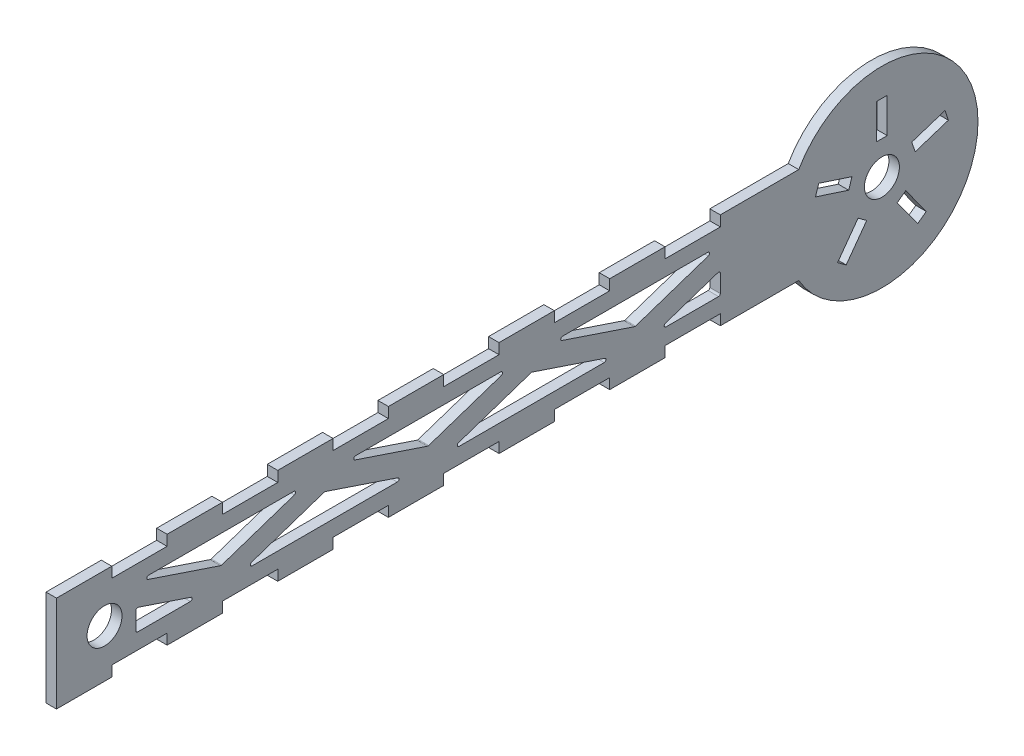
SolidWorks part; units mm, degrees
other "Markup1"
sketch "Sketch2" plane through (3, 13.75, 150) normal (0.7954, 0.3724, 0.4781) x (0.4726, 0.1125, -0.874)
ref_plane "Front Plane" through (0, 0, 0) normal (0, 0, 1) x (1, 0, 0)
ref_plane "Top Plane" through (0, 0, 0) normal (0, 1, 0) x (1, 0, 0)
ref_plane "Right Plane" through (0, 0, 0) normal (1, 0, 0) x (0, 0, -1)
sketch "Sketch1" plane through (0, 0, 0) normal (1, 0, 0) x (0, 0, -1)
  line L0 (65, -13.75) -> (65, 13.75) construction
  line L1 (-125, -13.75) -> (125, -13.75)
  line L2 (-125, -13.75) -> (-125, 13.75)
  line L3 (-125, 13.75) -> (125, 13.75)
  line L4 (125, -13.75) -> (125, 13.75)
  line L5 (-125, -13.75) -> (125, 13.75) construction
  line L6 (-125, 13.75) -> (125, -13.75) construction
  line L11 (119.8138, 4.386) -> (129.3244, 7.4762)
  line L13 (-125, 10.75) -> (-109.1667, 10.75) construction
  line L14 (-109.1667, 10.75) -> (-93.3333, 10.75)
  line L15 (-109.1667, 10.75) -> (-109.1667, 13.75)
  line L16 (-109.1667, 13.75) -> (-93.3333, 13.75)
  line L17 (-93.3333, 10.75) -> (-93.3333, 13.75)
  line L18 (-109.1667, 10.75) -> (-93.3333, 13.75) construction
  line L19 (-109.1667, 13.75) -> (-93.3333, 10.75) construction
  line L20 (-77.5, 10.75) -> (-61.6667, 10.75)
  line L21 (-77.5, 10.75) -> (-77.5, 13.75)
  line L22 (-77.5, 13.75) -> (-61.6667, 13.75)
  line L23 (-61.6667, 10.75) -> (-61.6667, 13.75)
  line L24 (-77.5, 10.75) -> (-61.6667, 13.75) construction
  line L25 (-77.5, 13.75) -> (-61.6667, 10.75) construction
  line L26 (-45.8333, 10.75) -> (-30, 10.75)
  line L27 (-45.8333, 10.75) -> (-45.8333, 13.75)
  line L28 (-45.8333, 13.75) -> (-30, 13.75)
  line L29 (-30, 10.75) -> (-30, 13.75)
  line L30 (-45.8333, 10.75) -> (-30, 13.75) construction
  line L31 (-45.8333, 13.75) -> (-30, 10.75) construction
  line L32 (-14.1667, 10.75) -> (1.6667, 10.75)
  line L33 (-14.1667, 10.75) -> (-14.1667, 13.75)
  line L34 (-14.1667, 13.75) -> (1.6667, 13.75)
  line L35 (1.6667, 10.75) -> (1.6667, 13.75)
  line L36 (-14.1667, 10.75) -> (1.6667, 13.75) construction
  line L37 (-14.1667, 13.75) -> (1.6667, 10.75) construction
  line L38 (17.5, 10.75) -> (33.3333, 10.75)
  line L39 (17.5, 10.75) -> (17.5, 13.75)
  line L40 (17.5, 13.75) -> (33.3333, 13.75)
  line L41 (33.3333, 10.75) -> (33.3333, 13.75)
  line L42 (17.5, 10.75) -> (33.3333, 13.75) construction
  line L43 (17.5, 13.75) -> (33.3333, 10.75) construction
  line L44 (49.1667, 10.75) -> (65, 10.75)
  line L45 (49.1667, 10.75) -> (49.1667, 13.75)
  line L46 (49.1667, 13.75) -> (65, 13.75)
  line L47 (65, 10.75) -> (65, 13.75)
  line L48 (49.1667, 10.75) -> (65, 13.75) construction
  line L49 (49.1667, 13.75) -> (65, 10.75) construction
  line L50 (-93.3333, 10.75) -> (-77.5, 10.75) construction
  line L51 (-61.6667, 10.75) -> (-45.8333, 10.75) construction
  line L52 (-30, 10.75) -> (-14.1667, 10.75) construction
  line L53 (1.6667, 10.75) -> (17.5, 10.75) construction
  line L54 (33.3333, 10.75) -> (49.1667, 10.75) construction
  line L56 (-125, 0) -> (125, 0) construction
  line L57 (49.1667, -13.75) -> (65, -13.75)
  line L58 (65, -10.75) -> (65, -13.75)
  line L59 (49.1667, -10.75) -> (65, -10.75)
  line L60 (49.1667, -10.75) -> (49.1667, -13.75)
  line L61 (17.5, -13.75) -> (33.3333, -13.75)
  line L62 (33.3333, -10.75) -> (33.3333, -13.75)
  line L63 (17.5, -10.75) -> (33.3333, -10.75)
  line L64 (17.5, -10.75) -> (17.5, -13.75)
  line L65 (-14.1667, -13.75) -> (1.6667, -13.75)
  line L66 (1.6667, -10.75) -> (1.6667, -13.75)
  line L67 (-14.1667, -10.75) -> (1.6667, -10.75)
  line L68 (-14.1667, -10.75) -> (-14.1667, -13.75)
  line L69 (-45.8333, -13.75) -> (-30, -13.75)
  line L70 (-30, -10.75) -> (-30, -13.75)
  line L71 (-45.8333, -10.75) -> (-30, -10.75)
  line L72 (-45.8333, -10.75) -> (-45.8333, -13.75)
  line L73 (-77.5, -13.75) -> (-61.6667, -13.75)
  line L74 (-61.6667, -10.75) -> (-61.6667, -13.75)
  line L75 (-77.5, -10.75) -> (-61.6667, -10.75)
  line L76 (-77.5, -10.75) -> (-77.5, -13.75)
  line L77 (-109.1667, -13.75) -> (-93.3333, -13.75)
  line L78 (-93.3333, -10.75) -> (-93.3333, -13.75)
  line L79 (-109.1667, -10.75) -> (-93.3333, -10.75)
  line L80 (-109.1667, -10.75) -> (-109.1667, -13.75)
  line L83 (109.725, 9.5) -> (112.775, 9.5)
  line L84 (109.725, 9.5) -> (109.725, 19.5)
  line L85 (109.725, 19.5) -> (112.775, 19.5)
  line L86 (112.775, 9.5) -> (112.775, 19.5)
  line L87 (109.725, 9.5) -> (112.775, 19.5) construction
  line L88 (109.725, 19.5) -> (112.775, 9.5) construction
  line L89 (119.8138, 4.386) -> (120.7563, 1.4853)
  line L90 (120.7563, 1.4853) -> (130.2669, 4.5755)
  line L91 (129.3244, 7.4762) -> (130.2669, 4.5755)
  line L92 (118.0677, -6.7893) -> (123.9456, -14.8795)
  line L93 (118.0677, -6.7893) -> (115.6002, -8.582)
  line L94 (115.6002, -8.582) -> (121.4781, -16.6722)
  line L95 (123.9456, -14.8795) -> (121.4781, -16.6722)
  line L96 (106.8998, -8.582) -> (101.0219, -16.6722)
  line L97 (106.8998, -8.582) -> (104.4323, -6.7893)
  line L98 (104.4323, -6.7893) -> (98.5544, -14.8795)
  line L99 (101.0219, -16.6722) -> (98.5544, -14.8795)
  line L100 (101.7437, 1.4853) -> (92.2331, 4.5755)
  line L101 (101.7437, 1.4853) -> (102.6862, 4.386)
  line L102 (102.6862, 4.386) -> (93.1756, 7.4762)
  line L103 (92.2331, 4.5755) -> (93.1756, 7.4762)
  line L104 (111.25, 0) -> (112.775, 9.5) construction
  circle A4 centre (111.25, 0) radius 5
  circle A5 centre (-111.25, 0) radius 5
  circle A7 centre (111.25, 0) radius 27.5
  point P0 (0, 0)
  point P6 (111.25, 14.5)
  point P13 (0, 0)
  point P14 (0, 0)
  point P19 (-101.25, 12.25)
  point P26 (-69.5833, 12.25)
  point P31 (-37.9167, 12.25)
  point P36 (-6.25, 12.25)
  point P41 (25.4167, 12.25)
  point P46 (57.0833, 12.25)
  point P54 (111.25, 0)
  point P96 (0, 0)
  dimension "D2" = 111.25
  dimension "D3" = 10
  dimension "D7" = 10
  dimension "D9" = 55
  dimension "D4" = 65
  dimension "D5" = 27.5
  dimension "D6" = 250
  dimension "D8" = 13.75
  dimension "D10" = 3
  dimension "D11" = 3.05
  dimension "D12" = 10
  dimension "D13" = 14.5
  dimension "D14" = 5
extrude "Boss-Extrude1" add sketch "Sketch1" along normal blind 3 contours L1 A7 L3 L84 L85 L86 L4 L11 L91 L90 L92 L95 L94 L96 L99 L98 | L3 A7 L1 L98 L97 L96 L94 L93 L92 L4 L90 L89 L11 L86 L83 L84 L100 L103 L102 L101 A4 | A7 L3 L47 L44 L45 L41 L38 L39 L35 L32 L33 L29 L26 L27 L23 L20 L21 L17 L14 L15 L2 L1 L80 L79 L78 L76 L75 L74 L72 L71 L70 L68 L67 L66 L64 L63 L62 L60 L59 L58
sketch "Sketch3" plane through (3, 0, 0) normal (1, 0, 0) x (0, 0, -1)
  line L0 (-101.7013, 6.25) -> (-102.25, 6.25) construction
  line L1 (-102.25, -6.25) -> (65, -6.25)
  line L2 (-102.25, -6.25) -> (-102.25, 6.25)
  line L3 (-102.25, 6.25) -> (65, 6.25)
  line L4 (65, -6.25) -> (65, 6.25)
  line L5 (-102.25, -6.25) -> (65, 6.25) construction
  line L6 (-102.25, 6.25) -> (65, -6.25) construction
  line L7 (-102.25, 6.25) -> (-102.25, 10.75) construction
  line L8 (65, 6.25) -> (64.4513, 6.25) construction
  line L9 (-102.25, -6.25) -> (-102.25, -10.75) construction
  line L10 (-102.25, 0) -> (-102.25, 6.25) construction
  line L11 (-102.25, 0) -> (-116.25, 0) construction
  line L12 (65, 10.75) -> (65, 13.75) construction
  line L13 (-109.1667, -10.75) -> (-93.3333, -10.75) construction
  line L14 (-102.25, 0) -> (-83.6184, -6.25)
  line L15 (-101.7013, 6.25) -> (-77.8529, -1.75)
  line L16 (-77.8529, -1.75) -> (-54.0045, 6.25)
  line L17 (-72.0874, -6.25) -> (-48.2389, 1.75)
  line L18 (-48.2389, 1.75) -> (-24.3905, -6.25)
  line L19 (-12.8595, -6.25) -> (10.9889, 1.75)
  line L20 (10.9889, 1.75) -> (34.8374, -6.25)
  line L21 (46.3684, -6.25) -> (65, 0)
  line L22 (-83.6184, -6.25) -> (-72.0874, -6.25) construction
  line L23 (-54.0045, 6.25) -> (-42.4734, 6.25) construction
  line L24 (-42.4734, 6.25) -> (-18.625, -1.75)
  line L25 (-18.625, -1.75) -> (5.2234, 6.25)
  line L26 (16.7545, 6.25) -> (40.6029, -1.75)
  line L27 (40.6029, -1.75) -> (64.4513, 6.25)
  line L28 (-24.3905, -6.25) -> (-12.8595, -6.25) construction
  line L29 (5.2234, 6.25) -> (16.7545, 6.25) construction
  line L30 (34.8374, -6.25) -> (46.3684, -6.25) construction
  line L31 (65, 0) -> (65, 6.25) construction
  circle A0 centre (-111.25, 0) radius 5 construction
  point P0 (-18.625, 0)
  point P18 (85.2212, 0)
  point P23 (0, 0)
  point P32 (0, 0)
  dimension "D1" = 4.5
  dimension "D2" = 14
  dimension "D3" = 6.1
  dimension "D4" = 8
extrude "Cut-Extrude1" cut sketch "Sketch3" against normal blind 3 contours L14 L2 L1 | L15 L16 L3 | L18 L17 L1 | L24 L25 L3 | L20 L19 L1 | L26 L27 L3 | L21 L1 L4
fillet "Fillet1" radius 0.5 21 edges at (1.5, -6.25, -46.3684) (1.5, 0, -65) (1.5, -6.25, -65) (1.5, -6.25, 24.3905) (1.5, -6.25, 72.0874) (1.5, -6.25, -34.8374) (1.5, -6.25, 12.8595) (1.5, 1.75, -10.9889) (1.5, 6.25, 42.4734) (1.5, 6.25, -16.7545) (1.5, -1.75, -40.6029) (1.5, -1.75, 18.625) (1.5, 6.25, -64.4513) (1.5, 6.25, -5.2234) (1.5, 1.75, 48.2389) (1.5, 6.25, 54.0045) (1.5, -1.75, 77.8529) (1.5, 6.25, 101.7013) (1.5, 0, 102.25) (1.5, -6.25, 83.6184) (1.5, -6.25, 102.25)
